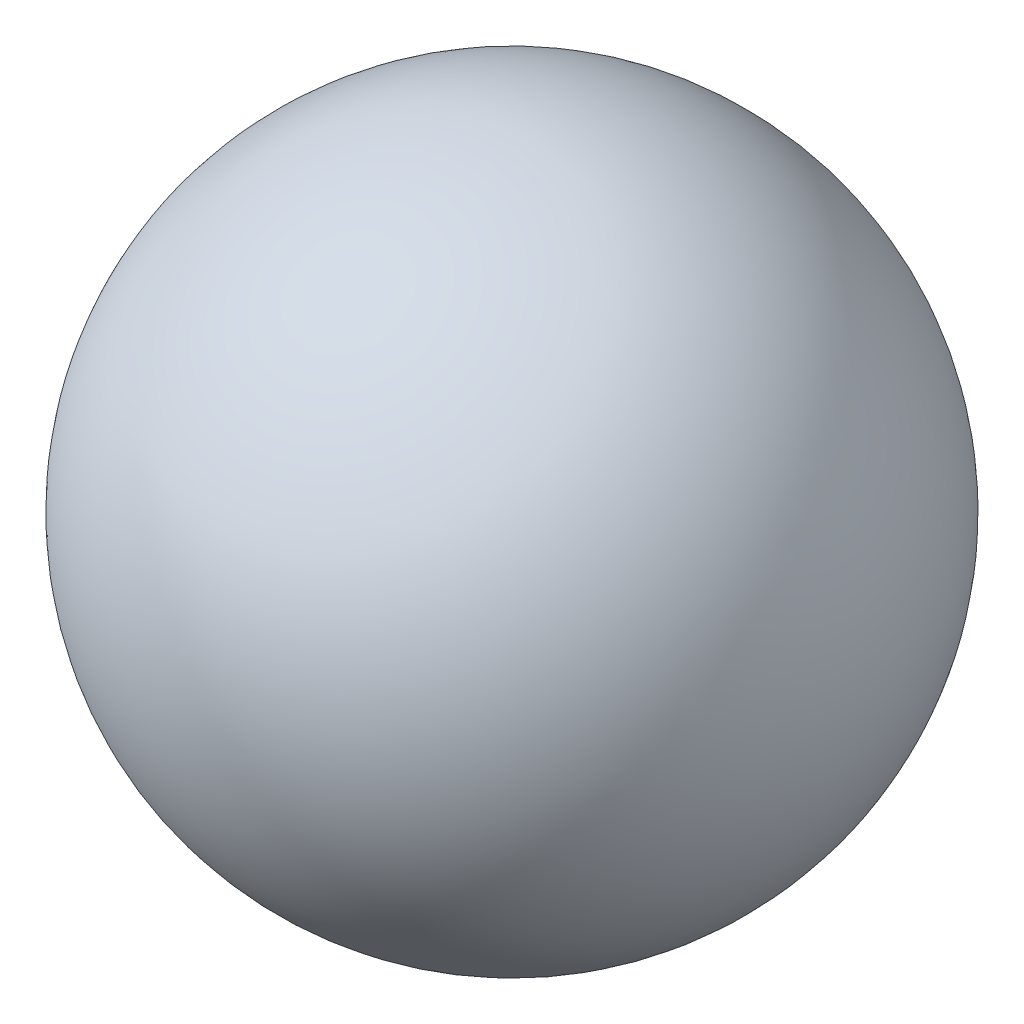
SolidWorks part; units mm, degrees
ref_plane "Front Plane" through (0, 0, 0) normal (0, 0, 1) x (1, 0, 0)
ref_plane "Top Plane" through (0, 0, 0) normal (0, 1, 0) x (1, 0, 0)
ref_plane "Right Plane" through (0, 0, 0) normal (1, 0, 0) x (0, 0, -1)
sketch "Sketch1" plane through (0, 0, 0) normal (0, 0, 1) x (1, 0, 0)
  line L0 (-12, 0) -> (12, 0)
  arc A0 (12, 0) -> (-12, 0) centre (0, 0) cw
  point P3 (0, 0)
  dimension "D2" = 12
  dimension "D1" = 24
revolve "Revolve1" add sketch "Sketch1" angle 360 about L0
